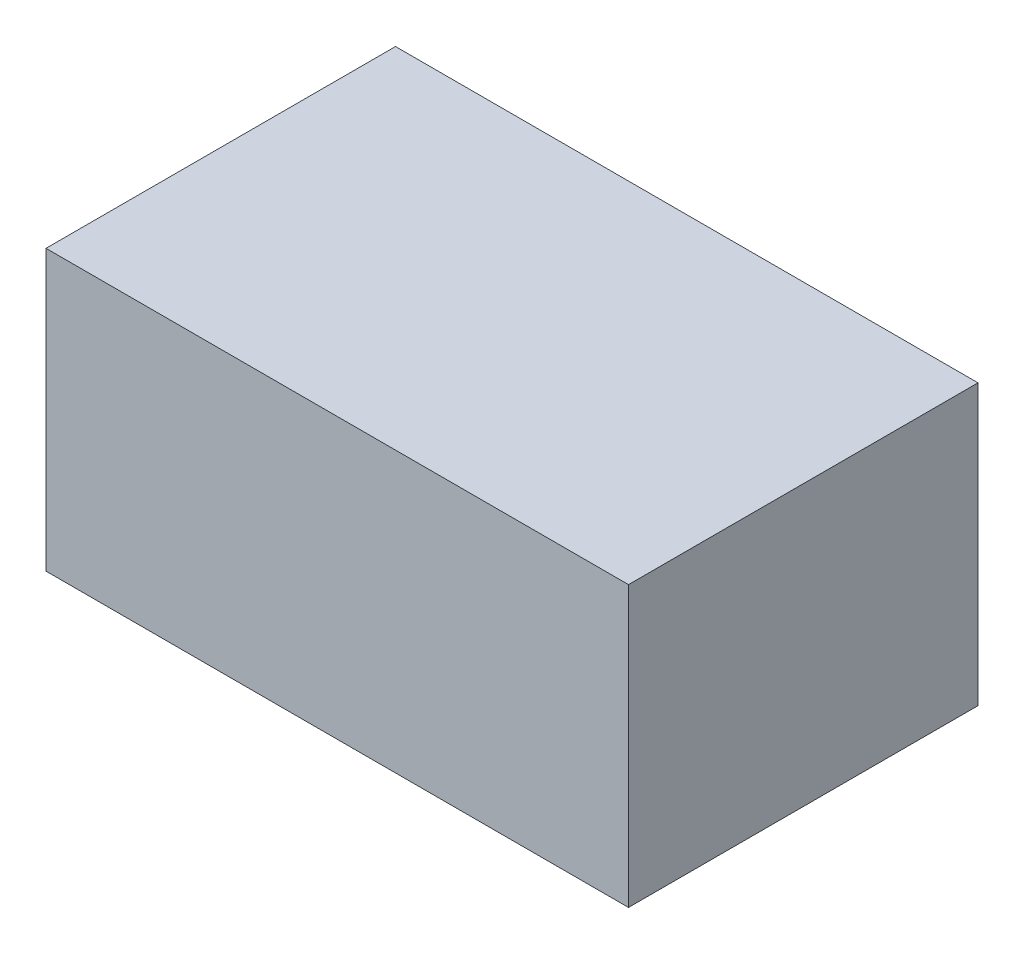
SolidWorks part; units mm, degrees
ref_plane "Front Plane" through (0, 0, 0) normal (0, 0, 1) x (1, 0, 0)
ref_plane "Top Plane" through (0, 0, 0) normal (0, 1, 0) x (1, 0, 0)
ref_plane "Right Plane" through (0, 0, 0) normal (1, 0, 0) x (0, 0, -1)
sketch "Sketch1" plane through (0, 0, 0) normal (0, 1, 0) x (1, 0, 0)
  line L1 (-3.75, 2.25) -> (3.75, 2.25)
  line L2 (-3.75, 2.25) -> (-3.75, -2.25)
  line L3 (-3.75, -2.25) -> (3.75, -2.25)
  line L4 (3.75, 2.25) -> (3.75, -2.25)
extrude "Boss-Extrude1" add sketch "Sketch1" along normal blind 3.6
